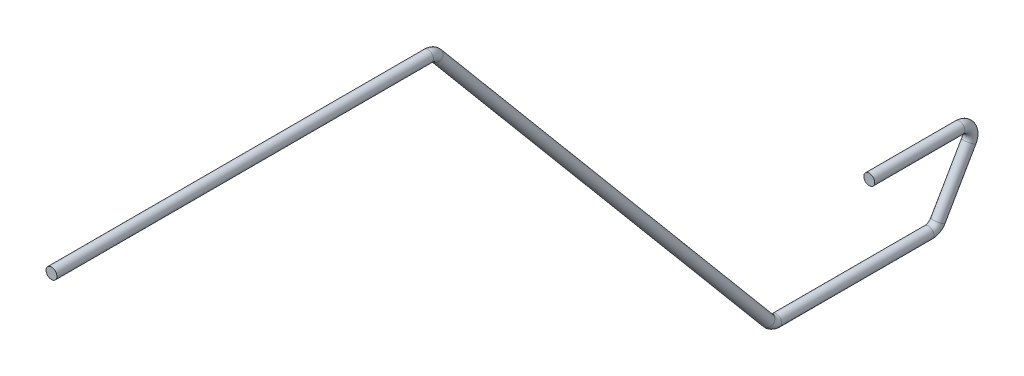
SolidWorks part; units mm, degrees
material "AISI 304"
ref_plane "Front Plane" through (0, 0, 0) normal (0, 0, 1) x (1, 0, 0)
ref_plane "Top Plane" through (0, 0, 0) normal (0, 1, 0) x (1, 0, 0)
ref_plane "Right Plane" through (0, 0, 0) normal (1, 0, 0) x (0, 0, -1)
sketch "Sketch1" plane through (0, 0, 0) normal (1, 0, 0) x (0, 0, -1)
  line L0 (0, 0) -> (17.5431, 0)
  line L1 (17.9323, -0.1815) -> (33.381, -18.5926)
  line L2 (33.7702, -18.7741) -> (40.86, -18.7741)
  line L3 (41.3, -18.5201) -> (42.7401, -16.0257)
  line L4 (42.3001, -15.2637) -> (38.1, -15.2637)
  arc A0 (42.7401, -16.0257) -> (42.3001, -15.2637) centre (42.3001, -15.7717) ccw
  arc A1 (40.86, -18.7741) -> (41.3, -18.5201) centre (40.86, -18.2661) ccw
  arc A2 (33.381, -18.5926) -> (33.7702, -18.7741) centre (33.7702, -18.2661) ccw
  arc A3 (17.5431, 0) -> (17.9323, -0.1815) centre (17.5431, -0.508) cw
  point P9 (43.18, -15.2637)
  point P12 (41.1533, -18.7741)
  point P15 (33.5333, -18.7741)
  point P18 (17.78, 0)
  dimension "D7" = 0.508
  dimension "D1" = 17.78
  dimension "D2" = 43.18
  dimension "D3" = 5.08
  dimension "D4" = 7.62
  dimension "D5" = 130
  dimension "D6" = 60
sweep "Sweep1" add path "Sketch1" circular profile diameter 0.508 parameters "D3"=0.508
